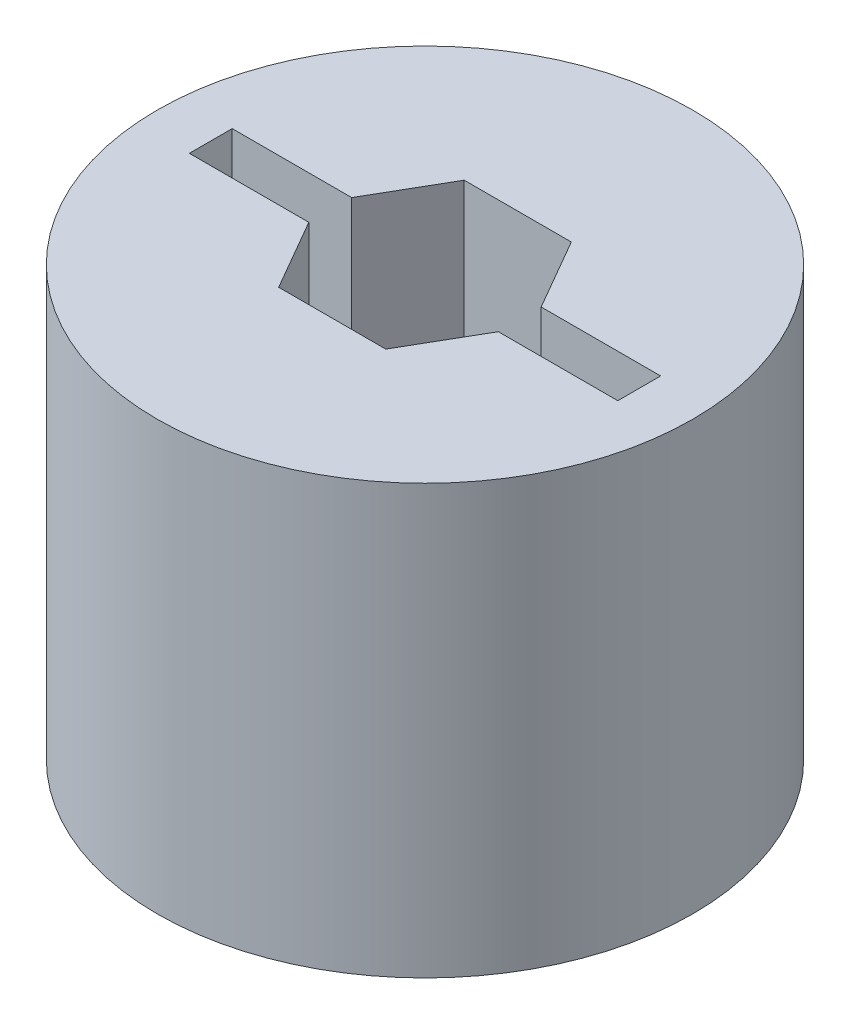
SolidWorks part; units mm, degrees
ref_plane "Front Plane" through (0, 0, 0) normal (0, 0, 1) x (1, 0, 0)
ref_plane "Top Plane" through (0, 0, 0) normal (0, 1, 0) x (1, 0, 0)
ref_plane "Right Plane" through (0, 0, 0) normal (1, 0, 0) x (0, 0, -1)
sketch "Sketch1" plane through (0, 0, 0) normal (0, 1, 0) x (1, 0, 0)
  circle A0 centre (0, 0) radius 15.875
  dimension "D1" = 31.75
extrude "Boss-Extrude1" add sketch "Sketch1" along normal blind 25.4
sketch "Sketch2" plane through (0, 25.4, 0) normal (0, 1, 0) x (1, 0, 0)
  line L1 (3.175, 5.4993) -> (-3.175, 5.4993)
  line L2 (-3.175, 5.4993) -> (-6.35, 0)
  line L3 (-6.35, 0) -> (-3.175, -5.4993)
  line L4 (-3.175, -5.4993) -> (3.175, -5.4993)
  line L5 (3.175, -5.4993) -> (6.35, 0)
  line L6 (6.35, 0) -> (3.175, 5.4993)
  line L7 (-12.7, -1.27) -> (12.7, -1.27)
  line L8 (-12.7, -1.27) -> (-12.7, 1.27)
  line L9 (-12.7, 1.27) -> (12.7, 1.27)
  line L10 (12.7, -1.27) -> (12.7, 1.27)
  line L11 (-12.7, -1.27) -> (12.7, 1.27) construction
  line L12 (-12.7, 1.27) -> (12.7, -1.27) construction
  circle A0 centre (0, 0) radius 5.4993 construction
  dimension "D1" = 6.35
  dimension "D2" = 25.4
  dimension "D3" = 2.54
extrude "Cut-Extrude1" cut sketch "Sketch2" against normal through all contours L9 L8 L7 L3 L2 | L7 L3 L4 L5 | L9 L2 L3 L7 L5 L6 | L2 L9 L6 L1 | L7 L10 L9 L6 L5
